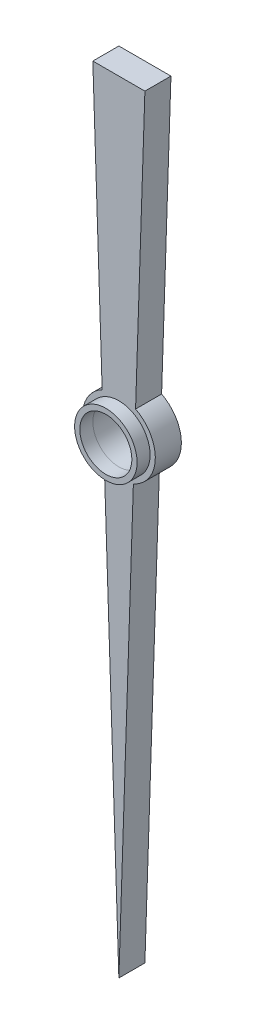
SolidWorks part; units mm, degrees
ref_plane "Plano frontal" through (0, 0, 0) normal (0, 0, 1) x (1, 0, 0)
ref_plane "Plano superior" through (0, 0, 0) normal (0, 1, 0) x (1, 0, 0)
ref_plane "Plano direito" through (0, 0, 0) normal (1, 0, 0) x (0, 0, -1)
sketch "Esboço1" plane through (0, 0, 0) normal (0, 0, 1) x (1, 0, 0)
  line L1 (0, 30) -> (1, 30)
  line L2 (0, 30) -> (-1, 30)
  line L3 (-1, 30) -> (-0.6415, 19.2444)
  line L4 (1, 30) -> (0.6415, 19.2444)
  line L6 (-0.5572, 16.7157) -> (0, 0)
  line L7 (0.5572, 16.7157) -> (0, 0)
  circle A1 centre (0, 18) radius 1
  arc A3 (-0.6415, 19.2444) -> (-0.5572, 16.7157) centre (0, 18) ccw
  arc A4 (0.5572, 16.7157) -> (0.6415, 19.2444) centre (0, 18) ccw
extrude "Ressalto-extrusão1" add sketch "Esboço1" along normal blind 1
sketch "Esboço3" plane through (0, 0, 1) normal (0, 0, 1) x (1, 0, 0)
  circle A0 centre (0, 18) radius 0.9991
  circle A1 centre (0, 18) radius 1.2
extrude "Ressalto-extrusão2" add sketch "Esboço3" along normal blind 0.5
